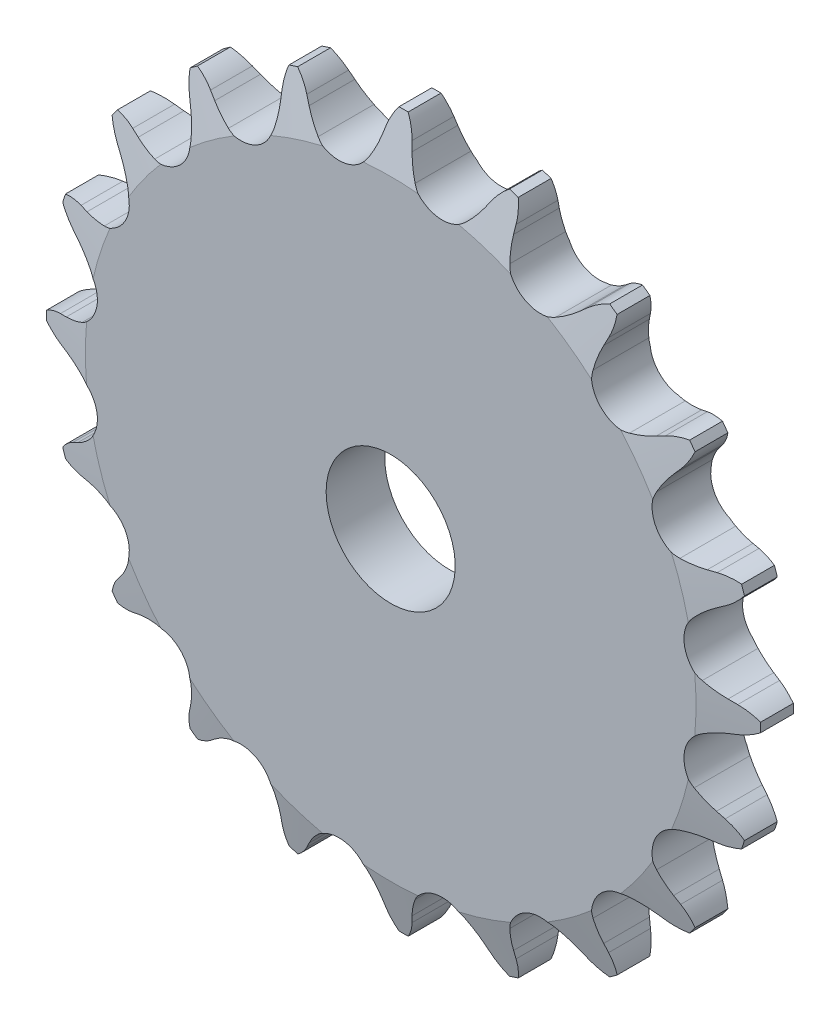
SolidWorks part; units mm, degrees
ref_plane "Front Plane" through (0, 0, 0) normal (0, 0, 1) x (1, 0, 0)
ref_plane "Top Plane" through (0, 0, 0) normal (0, 1, 0) x (1, 0, 0)
ref_plane "Right Plane" through (0, 0, 0) normal (1, 0, 0) x (0, 0, -1)
sketch "Sketch0" plane through (0, 0, 0) normal (0, 0, 1) x (1, 0, 0)
  line L0 (6.35, -40.0923) -> (0, 0) construction
  line L1 (0, 0) -> (18.4284, -36.1678) construction
  line L2 (0, 0) -> (-6.35, -40.0923) construction
  line L3 (6.35, -40.0923) -> (18.4284, -36.1678) construction
  line L4 (6.35, -40.0923) -> (-6.35, -40.0923) construction
  line L5 (11.3499, -40.1061) -> (10.8313, -39.2696)
  line L6 (6.35, -40.0923) -> (0, -41.0981) construction
  line L7 (1.5991, -41.6505) -> (1.8339, -40.6947)
  line L8 (0, -40.0923) -> (0, -43.9023) construction
  line L9 (9.0918, -37.1521) -> (2.0262, -44.729) construction
  line L10 (0, 0) -> (0, -40.0923) construction
  line L11 (10.8313, -39.2696) -> (2.0262, -44.729) construction
  line L12 (0, -43.9023) -> (0, -44.5822) construction
  line L13 (16.9017, -36.6639) -> (11.3499, -40.1061) construction
  circle A0 centre (0, 0) radius 43.9023 construction
  circle A1 centre (0, 0) radius 40.5921 construction
  arc A2 (-5.5124, -46.5794) -> (19.6365, -42.5962) centre (0, 0) ccw
  circle A3 centre (0, 0) radius 44.5822 construction
  circle A4 centre (6.35, -40.0923) radius 3.9624 construction
  arc A7 (9.0918, -37.1521) -> (2.8338, -38.1432) centre (6.35, -40.0923) ccw
  circle A8 centre (6.35, -40.0923) radius 4.0203 construction
  arc A9 (11.3499, -40.1061) -> (19.6365, -42.5962) centre (16.9017, -36.6639) ccw
  arc A10 (10.8313, -39.2696) -> (9.0918, -37.1521) centre (2.0262, -44.729) ccw
  arc A11 (1.5991, -41.6505) -> (-5.5124, -46.5794) centre (-4.7447, -40.0923) cw
  arc A12 (1.8339, -40.6947) -> (2.8338, -38.1432) centre (11.8949, -43.1659) cw
  dimension "D1" = 4.0203
  dimension "Dr" = 7.9248
  dimension "Ds" = 8.0406
  dimension "R" = 4.0203
  dimension "Pitch" = 12.7
  dimension "A" = 38
  dimension "360/N" = 18
  dimension "B" = 15.2
  dimension "ab" = 11.0947
  dimension "J" = 3.81
  dimension "ac" = 6.3398
sketch "Sketch1" plane through (0, 0, 0) normal (1, 0, 0) x (0, 0, -1)
  line L0 (3.6068, 0) -> (-3.6068, 0)
  line L1 (-3.6068, 0) -> (-3.6068, 37.5523)
  line L2 (-3.6068, 37.5523) -> (-2.0193, 43.9023)
  line L3 (-2.0193, 43.9023) -> (2.0193, 43.9023)
  line L4 (2.0193, 43.9023) -> (3.6068, 37.5523)
  line L5 (3.6068, 37.5523) -> (3.6068, 0)
  line L7 (0, 43.9023) -> (0, 0) construction
  line L8 (-3.6068, 37.5523) -> (3.6068, 37.5523) construction
  line L9 (0, 43.9023) -> (0, -43.9023) construction
  line L10 (-3.6068, 37.5523) -> (-3.6068, 43.9023) construction
  line L11 (-3.6068, 43.9023) -> (-2.0193, 43.9023) construction
  line L12 (2.0193, 43.9023) -> (3.6068, 43.9023) construction
  line L13 (3.6068, 43.9023) -> (3.6068, 37.5523) construction
  dimension "t" = 7.2136
  dimension "g" = 1.5875
  dimension "h" = 6.35
revolve "Revolve1" add sketch "Sketch1" angle 360 mid plane about L0
extrude "Cut-Extrude1" cut sketch "Sketch0" against normal through all and the other way through all
pattern_circular "CirPattern1" count 20 over 360 about axis through (0, 0, 0) along (0, 0, 1) of "Cut-Extrude1"
sketch "Sketch2" plane through (0, 0, 0) normal (0, 0, 1) x (1, 0, 0)
  circle A0 centre (0, 0) radius 7.9375 construction
  circle A1 centre (0, 0) radius 30.1625
  circle A2 centre (0, 0) radius 43.942 construction
  dimension "Bore" = 15.875
  dimension "Hub Dia." = 60.325
  dimension "OD" = 87.884
sketch "Sketch3" plane through (0, 0, 0) normal (0, 0, 1) x (1, 0, 0)
  circle A0 centre (0, 0) radius 7.9375 construction
  circle A1 centre (0, 0) radius 7.9375
  circle A2 centre (0, 0) radius 43.942 construction
  circle A3 centre (0, 0) radius 43.942
extrude "Cut-Extrude2" cut sketch "Sketch3" along normal through all and the other way through all flip side to cut
equation "\"360/N@Sketch0\" = 360/\"Teeth@CirPattern1\""
equation "\"Ds@Sketch0\" = 1.005 * \"Dr@Sketch0\" + 0.003"
equation "\"R@Sketch0\" = 1/2 * \"Ds@Sketch0\""
equation "\"A@Sketch0\" = 35 +  ( 60 / \"Teeth@CirPattern1\" ) "
equation "\"B@Sketch0\" = 18 -  ( 56 / \"Teeth@CirPattern1\" )"
equation "\"ac@Sketch0\" = 0.8 * \"Dr@Sketch0\""
equation "\"ab@Sketch0\" = 1.4 * \"Dr@Sketch0\""
equation "\"J@Sketch0\" = 0.3 * \"Pitch@Sketch0\""
equation "\"h@Sketch1\" = \"Pitch@Sketch0\" / 2"
equation "\"g@Sketch1\" = \"h@Sketch1\" / 4"
